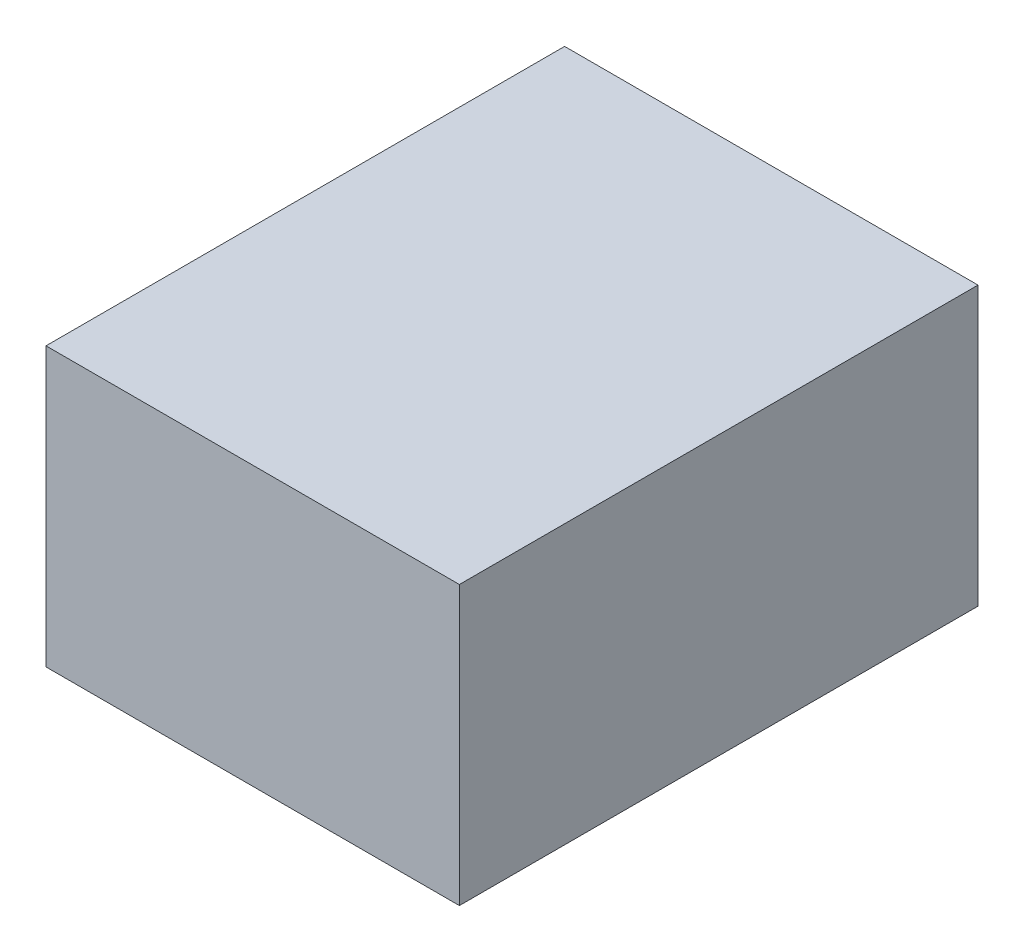
SolidWorks part; units mm, degrees
ref_plane "前视基准面" through (0, 0, 0) normal (0, 0, 1) x (1, 0, 0)
ref_plane "上视基准面" through (0, 0, 0) normal (0, 1, 0) x (1, 0, 0)
ref_plane "右视基准面" through (0, 0, 0) normal (1, 0, 0) x (0, 0, -1)
sketch "草图1" plane through (0, 0, 0) normal (0, 0, 1) x (1, 0, 0)
  line L1 (27.5, -18.5) -> (-27.5, -18.5)
  line L2 (27.5, -18.5) -> (27.5, 18.5)
  line L3 (27.5, 18.5) -> (-27.5, 18.5)
  line L4 (-27.5, -18.5) -> (-27.5, 18.5)
  line L5 (27.5, -18.5) -> (-27.5, 18.5) construction
  line L6 (27.5, 18.5) -> (-27.5, -18.5) construction
  point P0 (0, 0)
  dimension "D1" = 55
  dimension "D2" = 37
extrude "凸台-拉伸1" add sketch "草图1" along normal blind 69
